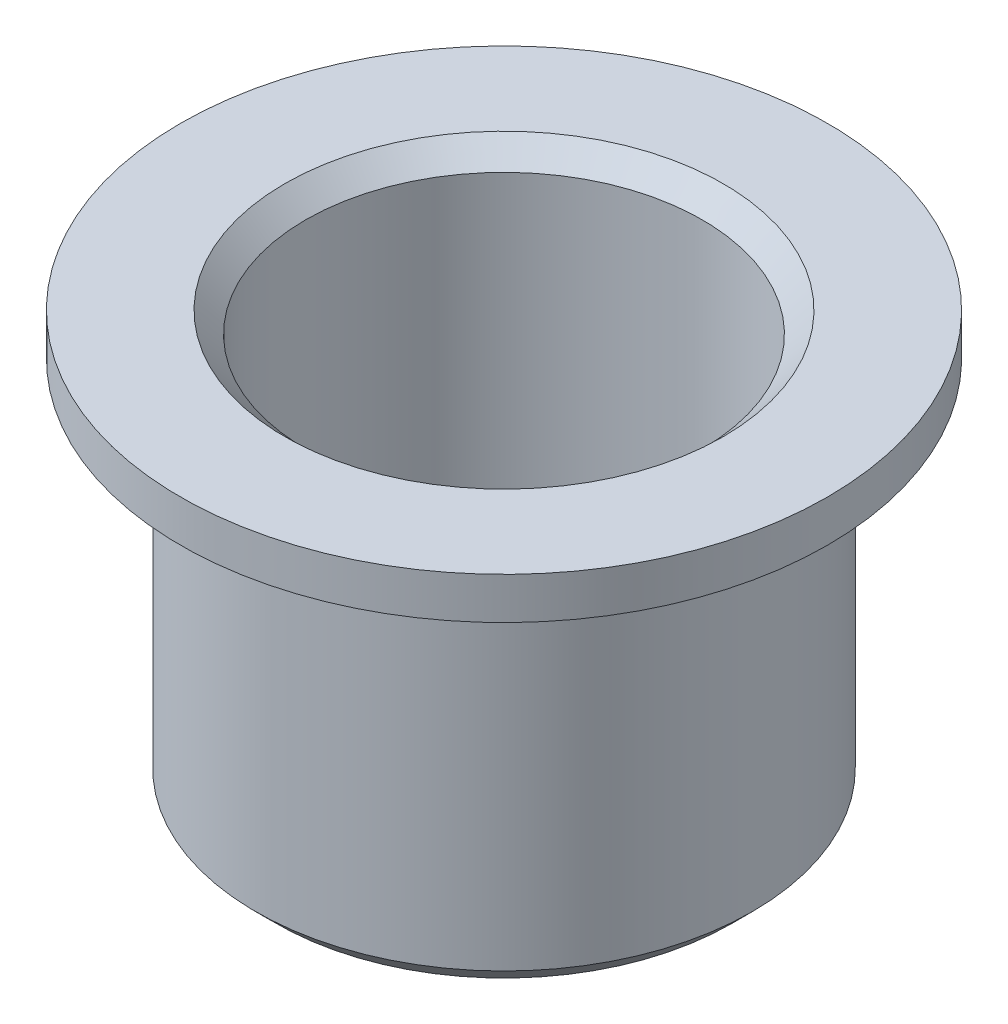
SolidWorks part; units mm, degrees
ref_plane "Front Plane" through (0, 0, 0) normal (0, 0, 1) x (1, 0, 0)
ref_plane "Top Plane" through (0, 0, 0) normal (0, 1, 0) x (1, 0, 0)
ref_plane "Right Plane" through (0, 0, 0) normal (1, 0, 0) x (0, 0, -1)
sketch "Sketch1" plane through (0, 0, 0) normal (0, 0, 1) x (1, 0, 0)
  line L0 (0, -12.9233) -> (0, 12.9233) construction
  line L1 (-19.3603, 0) -> (19.3603, 0) construction
  line L2 (4.75, 9.5) -> (4.75, 0)
  line L3 (5.25, 10) -> (7.75, 10)
  line L4 (7.75, 10) -> (7.75, 9)
  line L5 (7.75, 9) -> (5.95, 7.9608)
  line L6 (5.45, 0) -> (4.75, 0)
  line L7 (5.95, 0.5) -> (5.45, 0)
  line L8 (5.95, 7.9608) -> (5.95, 0.5)
  line L9 (4.75, 9.5) -> (5.25, 10)
  point P0 (4.75, 10)
  point P4 (0, 0)
  point P7 (0, 0)
  point P9 (5.95, 0)
  dimension "D1" = 4.75
  dimension "D2" = 3
  dimension "D3" = 10
  dimension "D4" = 1
  dimension "D5" = 5.95
  dimension "D6" = 30
revolve "Revolve1" add sketch "Sketch1" angle 360 about L0
